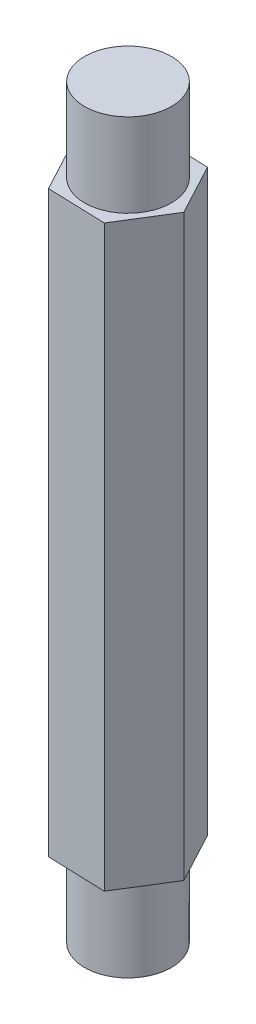
SolidWorks part; units mm, degrees
material "Brass"
ref_plane "Front Plane" through (0, 0, 0) normal (0, 0, 1) x (1, 0, 0)
ref_plane "Top Plane" through (0, 0, 0) normal (0, 1, 0) x (1, 0, 0)
ref_plane "Right Plane" through (0, 0, 0) normal (1, 0, 0) x (0, 0, -1)
sketch "Sketch1" plane through (0, 0, 0) normal (0, 1, 0) x (1, 0, 0)
  line L1 (1.0344, -1.9348) -> (2.1928, -0.0715)
  line L2 (2.1928, -0.0715) -> (1.1583, 1.8632)
  line L3 (1.1583, 1.8632) -> (-1.0344, 1.9348)
  line L4 (-1.0344, 1.9348) -> (-2.1928, 0.0715)
  line L5 (-2.1928, 0.0715) -> (-1.1583, -1.8632)
  line L6 (-1.1583, -1.8632) -> (1.0344, -1.9348)
  circle A0 centre (0, 0) radius 1.9 construction
  dimension "D1" = 1.9
extrude "Boss-Extrude1" add sketch "Sketch1" along normal blind 22
sketch "Sketch2" plane through (0, 22, 0) normal (0, 1, 0) x (1, 0, 0)
  circle A0 centre (0, 0) radius 1.65
  dimension "D1" = 3.3
extrude "Boss-Extrude2" add sketch "Sketch2" along normal blind 3.175 contours A0
sketch "Sketch3" plane through (0, 0, 0) normal (0, -1, 0) x (1, 0, 0)
  circle A0 centre (0, 0) radius 1.65
  dimension "D1" = 3.3
extrude "Boss-Extrude3" add sketch "Sketch3" along normal blind 3.175
